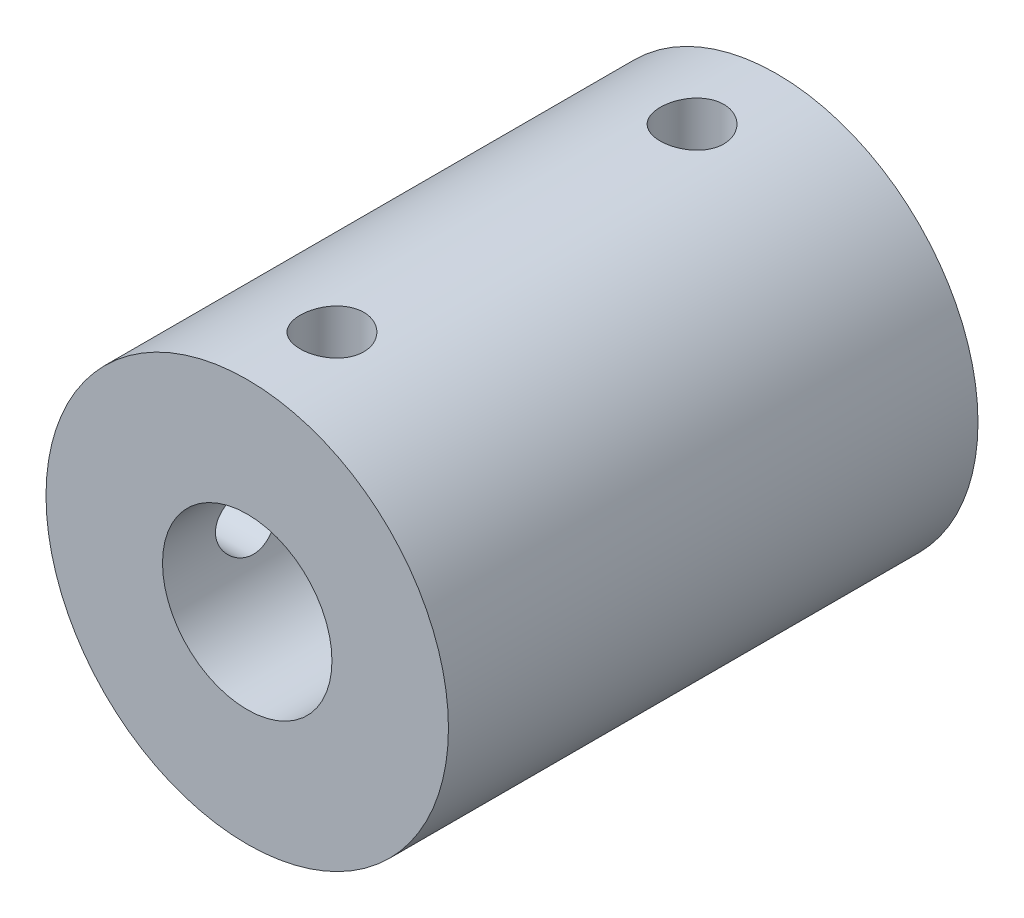
SolidWorks part; units mm, degrees
ref_plane "Plano frontal" through (0, 0, 0) normal (0, 0, 1) x (1, 0, 0)
ref_plane "Plano superior" through (0, 0, 0) normal (0, 1, 0) x (1, 0, 0)
ref_plane "Plano direito" through (0, 0, 0) normal (1, 0, 0) x (0, 0, -1)
sketch "Esboço1" plane through (0, 0, 0) normal (0, 0, 1) x (1, 0, 0)
  circle A0 centre (0, 0) radius 9.5
  dimension "D1" = 19
extrude "Ressalto-extrusão1" add sketch "Esboço1" along normal blind 25
sketch "Esboço2" plane through (0, 0, 25) normal (0, 0, 1) x (1, 0, 0)
  circle A0 centre (0, 0) radius 4
  dimension "D1" = 8
extrude "Corte-extrusão1" cut sketch "Esboço2" against normal blind 12.5
sketch "Esboço3" plane through (0, 0, 0) normal (0, 0, -1) x (-1, 0, 0)
  circle A0 centre (0, 0) radius 2.5
  dimension "D1" = 5
extrude "Corte-extrusão2" cut sketch "Esboço3" against normal through all
sketch "Esboço4" plane through (0, 0, 0) normal (0, 1, 0) x (1, 0, 0)
  line L0 (-10.6584, -12.5) -> (12.1285, -12.5) construction
  line L1 (0, -26.8074) -> (0, 1.6446) construction
  line L2 (2.5, 0) -> (-2.5, 0) construction
  circle A0 centre (0, -4) radius 1.5
  circle A1 centre (0, -21) radius 1.5
  dimension "D2" = 3
  dimension "D1" = 4
extrude "Corte-extrusão3" cut sketch "Esboço4" along normal blind 12
sketch "Esboço5" plane through (0, 0, 0) normal (1, 0, 0) x (0, 0, -1)
  line L0 (-26.9029, 0) -> (5.1486, 0) construction
  line L1 (-12.5, -10.6906) -> (-12.5, 10.5917) construction
  line L2 (-25, 9.5) -> (-25, -9.5) construction
  circle A0 centre (-21, 0) radius 1.5
  circle A1 centre (-4, 0) radius 1.5
  dimension "D1" = 3
  dimension "D2" = 4
extrude "Corte-extrusão4" cut sketch "Esboço5" against normal through all
